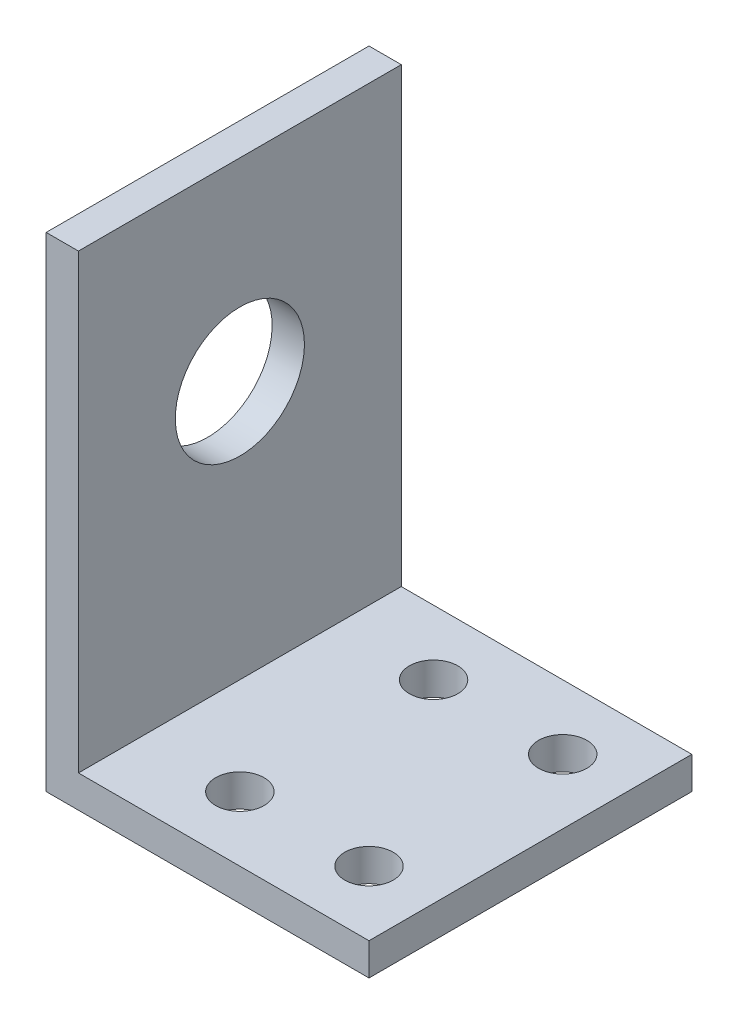
SolidWorks part; units mm, degrees
ref_plane "Front" through (0, 0, 0) normal (0, 0, 1) x (1, 0, 0)
ref_plane "Top" through (0, 0, 0) normal (0, 1, 0) x (1, 0, 0)
ref_plane "Right" through (0, 0, 0) normal (1, 0, 0) x (0, 0, -1)
sketch "草图1" plane through (0, 0, 0) normal (0, 0, 1) x (1, 0, 0)
  line L0 (0, 0) -> (0, 38)
  line L1 (0, 38) -> (3, 38)
  line L2 (3, 38) -> (3, 3)
  line L3 (3, 3) -> (20, 3)
  line L4 (20, 3) -> (20, 0)
  line L5 (20, 0) -> (0, 0)
  dimension "D1" = 38
  dimension "D2" = 3
  dimension "D3" = 35
  dimension "D4" = 17
extrude "凸台-拉伸1" add sketch "草图1" along normal blind 20
sketch "草图2" plane through (0, 3, 0) normal (0, 1, 0) x (1, 0, 0)
  line L0 (16, 0) -> (16, -20) construction
  line L1 (20, 0) -> (3, 0) construction
  line L2 (20, -20) -> (3, -20) construction
  line L3 (20, -20) -> (20, 0) construction
  circle A0 centre (16, -16) radius 1.5
  circle A1 centre (16, -4) radius 1.5
  dimension "D2" = 3
  dimension "D3" = 3
  dimension "D1" = 4
  dimension "D4" = 12
  dimension "D5" = 4
extrude "切除-拉伸1" cut sketch "草图2" against normal through all
sketch "草图3" plane through (3, 0, 0) normal (1, 0, 0) x (0, 0, -1)
  circle A0 centre (-10, 18) radius 4
  dimension "D1" = 8
extrude "切除-拉伸2" cut sketch "草图3" against normal through all
sketch "草图4" plane through (0, 3, 0) normal (0, 1, 0) x (1, 0, 0)
  circle A0 centre (8, -16) radius 1.5
  circle A1 centre (8, -4) radius 1.5
  dimension "D3" = 3
extrude "切除-拉伸3" cut sketch "草图4" against normal blind 20
sketch "草图5" plane through (0, 38, 0) normal (0, 1, 0) x (1, 0, 0)
  line L0 (3, -20) -> (3, 0) construction
  line L1 (3, 0) -> (0, 0)
  line L2 (3, 0) -> (3, -20)
  line L3 (3, -20) -> (0, -20)
  line L4 (0, 0) -> (0, -20)
  line L5 (3, 0) -> (0, 0) construction
  line L6 (3, -20) -> (0, -20) construction
  line L7 (0, -20) -> (0, 0) construction
extrude "切除-拉伸4" cut sketch "草图5" against normal blind 8
sketch "草图6" plane through (3, 0, 0) normal (1, 0, 0) x (0, 0, -1)
  line L0 (-20, 30) -> (0, 30) construction
  line L1 (0, 3) -> (-20, 3)
  line L2 (0, 3) -> (0, 30)
  line L3 (0, 30) -> (-20, 30)
  line L4 (-20, 3) -> (-20, 30)
  line L5 (-20, 3) -> (-20, 30) construction
extrude "切除-拉伸5" cut sketch "草图6" against normal blind 1
sketch "草图7" plane through (0, 3, 0) normal (0, 1, 0) x (1, 0, 0)
  line L0 (2, -20) -> (2, 0) construction
  line L1 (2, 0) -> (20, 0)
  line L2 (2, 0) -> (2, -20)
  line L3 (2, -20) -> (20, -20)
  line L4 (20, 0) -> (20, -20)
  line L5 (20, 0) -> (2, 0) construction
  line L6 (20, -20) -> (2, -20) construction
extrude "切除-拉伸6" cut sketch "草图7" against normal blind 1
